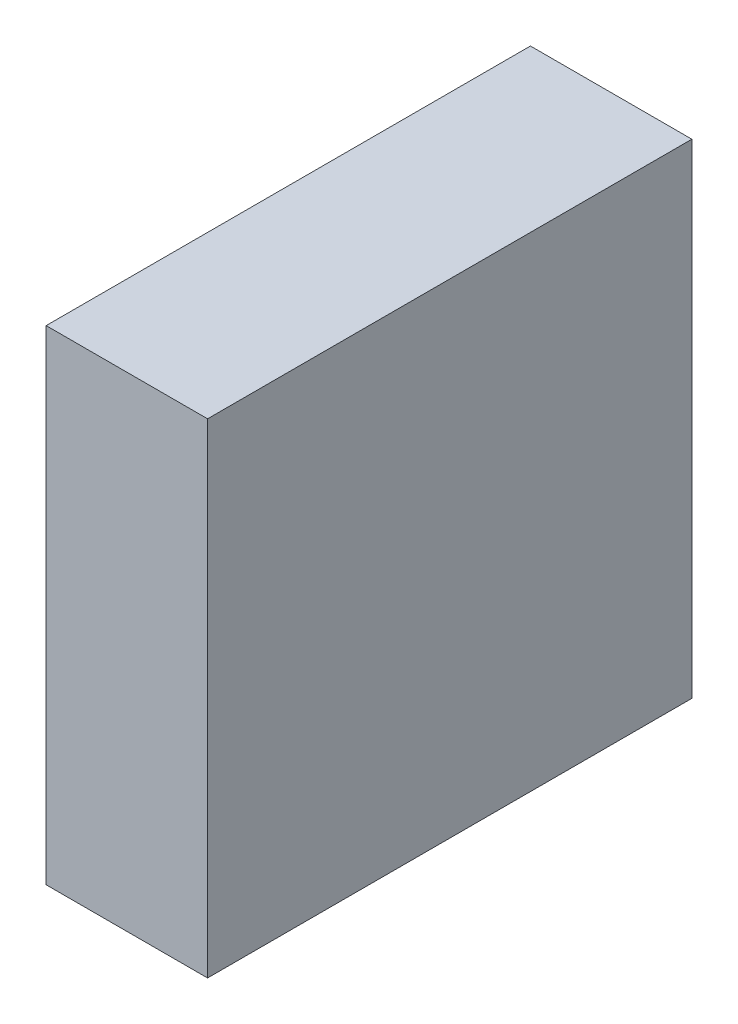
SolidWorks part; units mm, degrees
ref_plane "Front Plane" through (0, 0, 0) normal (0, 0, 1) x (1, 0, 0)
ref_plane "Top Plane" through (0, 0, 0) normal (0, 1, 0) x (1, 0, 0)
ref_plane "Right Plane" through (0, 0, 0) normal (1, 0, 0) x (0, 0, -1)
sketch "Sketch1" plane through (0, 0, 0) normal (0, 1, 0) x (1, 0, 0)
  line L0 (0, 0) -> (0, 9)
  line L1 (0, 0) -> (3, 0)
  line L2 (3, 0) -> (3, 9)
  line L3 (3, 9) -> (0, 9)
extrude "Boss-Extrude1" add sketch "Sketch1" along normal blind 9
